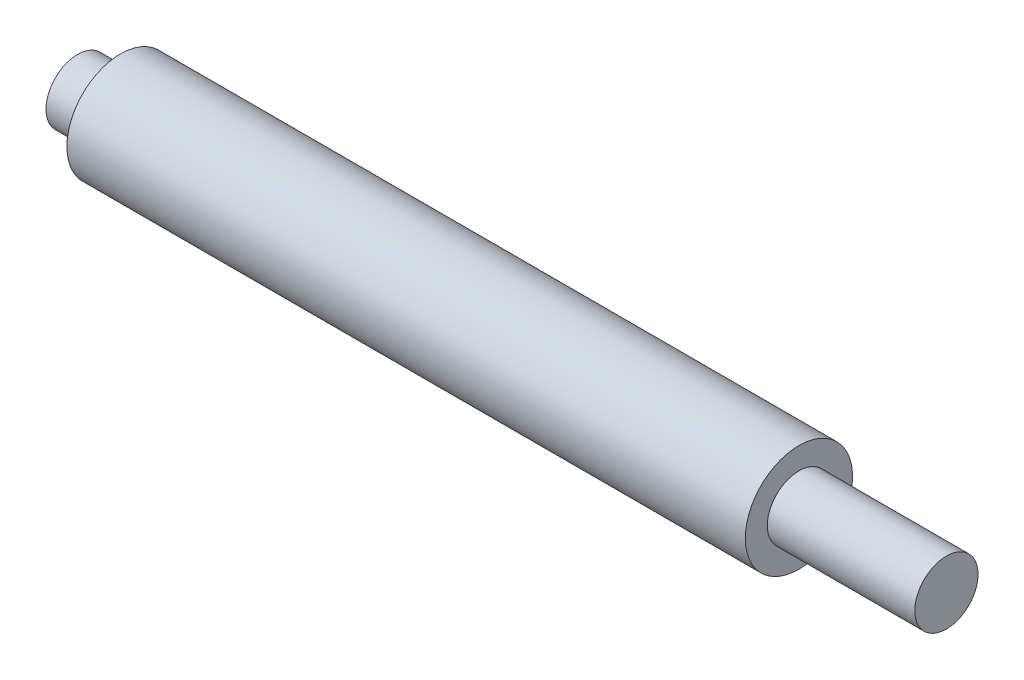
SolidWorks part; units mm, degrees
ref_plane "Front Plane" through (0, 0, 0) normal (0, 0, 1) x (1, 0, 0)
ref_plane "Top Plane" through (0, 0, 0) normal (0, 1, 0) x (1, 0, 0)
ref_plane "Right Plane" through (0, 0, 0) normal (1, 0, 0) x (0, 0, -1)
sketch "Sketch1" plane through (0, 0, 0) normal (0, 0, 1) x (1, 0, 0)
  line L0 (0, 0) -> (81, 0)
  line L1 (81, 0) -> (81, 2.95)
  line L2 (81, 2.95) -> (67.25, 2.95)
  line L3 (67.25, 2.95) -> (67.25, 5)
  line L4 (67.25, 5) -> (4, 5)
  line L5 (4, 5) -> (4, 2.95)
  line L6 (4, 2.95) -> (0, 2.95)
  line L7 (0, 2.95) -> (0, 0)
  dimension "D1" = 4
  dimension "D2" = 13.75
  dimension "D3" = 2.95
  dimension "D4" = 81
  dimension "D5" = 5
revolve "Revolve1" add sketch "Sketch1" angle 360 about L0
